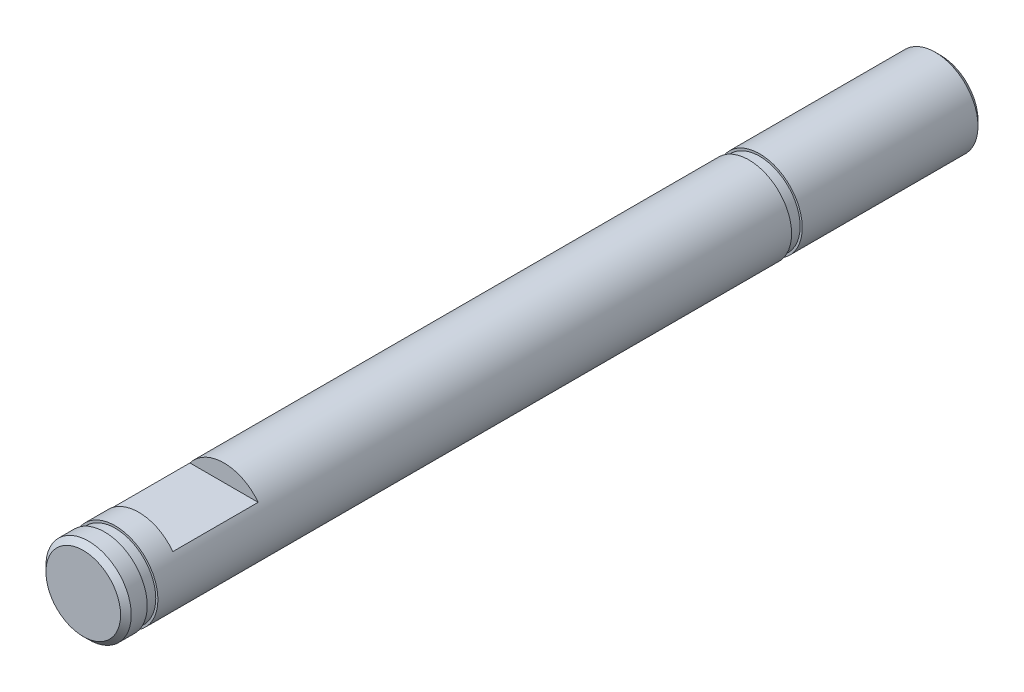
SolidWorks part; units mm, degrees
material "Acier allié inoxydable"
ref_plane "Plan de face" through (0, 0, 0) normal (0, 0, 1) x (1, 0, 0)
ref_plane "Plan de dessus" through (0, 0, 0) normal (0, 1, 0) x (1, 0, 0)
ref_plane "Plan de droite" through (0, 0, 0) normal (1, 0, 0) x (0, 0, -1)
sketch "Circle" plane through (0, 0, 0) normal (0, 0, 1) x (1, 0, 0)
  circle A0 centre (0, 0) radius 2
extrude "Boss.-Extru.1" add sketch "Circle" along normal blind 40.2
ref_plane "PlanMeplatPolulu" through (0, 0, 37.6) normal (0, 0, 1) x (1, 0, 0)
sketch "MeplatPololu" plane through (0, 0, 37.6) normal (0, 0, 1) x (1, 0, 0)
  line L0 (-1.6, 1.2) -> (1.6, 1.2)
  circle A0 centre (0, 0) radius 2 construction
  arc A1 (1.6, 1.2) -> (-1.6, 1.2) centre (0, 0) ccw
  dimension "D1" = 1.2
extrude "Enlèv. mat.-Extru.1" cut sketch "MeplatPololu" against normal blind 4
ref_plane "PlanMeplatRoueDentee" through (0, 0, 17.09) normal (0, 0, 1) x (1, 0, 0)
sketch "MeplatRoueDentee" plane through (0, 0, 17.09) normal (0, 0, 1) x (1, 0, 0)
  line L0 (0.1646, -1.9932) -> (-1.9596, 0.4001)
  line L1 (0, 0) -> (-0.8975, -0.7966) construction
  line L2 (0, 0.0244) -> (0, 50000.0244) construction
  line L4 (-1.6, 1.2) -> (1.6, 1.2) construction
  circle A0 centre (0, 0) radius 2 construction
  arc A1 (1.6, 1.2) -> (-1.6, 1.2) centre (0, 0) ccw construction
  arc A2 (-1.9596, 0.4001) -> (0.1646, -1.9932) centre (0, 0) ccw
  dimension "D1" = 1.2
  dimension "D2" = 131.59
extrude "Enlèv. mat.-Extru.2" cut sketch "MeplatRoueDentee" against normal blind 5
ref_plane "PlanGorgeCirclipPolulu" through (0, 0, 38.7) normal (0, 0, 1) x (1, 0, 0)
sketch "GorgeCirclipPolulu" plane through (0, 0, 38.7) normal (0, 0, 1) x (1, 0, 0)
  circle A0 centre (0, 0) radius 1.9
extrude "Enlèv. mat.-Extru.3" cut sketch "GorgeCirclipPolulu" along normal blind 0.5 flip side to cut
ref_plane "PlanGorgeCirclipPoulie" through (0, 0, 8.99) normal (0, 0, 1) x (1, 0, 0)
sketch "Esquisse1" plane through (0, 0, 8.99) normal (0, 0, 1) x (1, 0, 0)
  circle A0 centre (0, 0) radius 1.9
extrude "Enlèv. mat.-Extru.4" cut sketch "Esquisse1" against normal blind 0.5 flip side to cut
chamfer "Chanfrein1" distance 0.25 angle 45 1 edges at (2, 0, 40.2)
chamfer "Chanfrein2" distance 0.25 angle 45 1 edges at (2, 0, 0)
